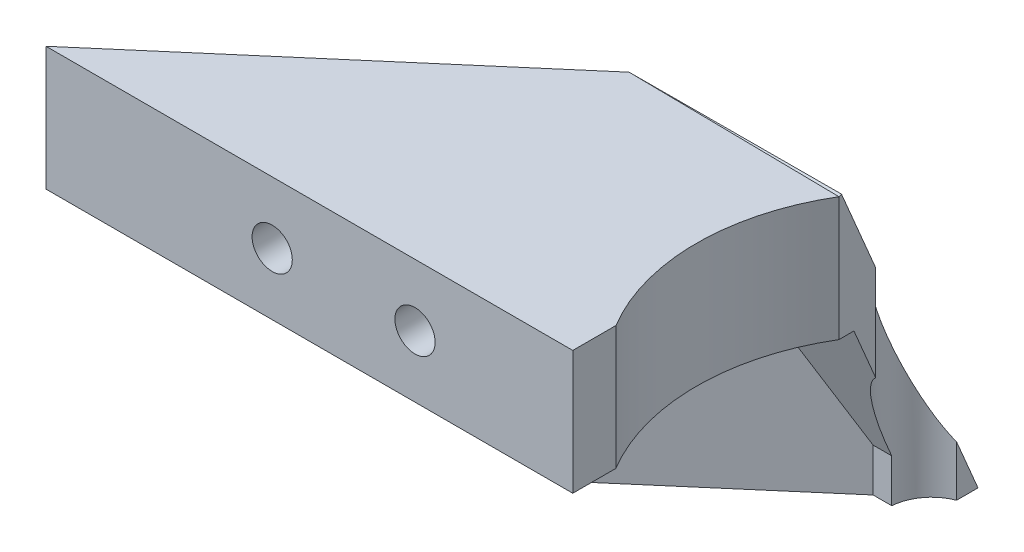
SolidWorks part; units mm, degrees
ref_plane "Alzado" through (0, 0, 0) normal (0, 0, 1) x (1, 0, 0)
ref_plane "Planta" through (0, 0, 0) normal (0, 1, 0) x (1, 0, 0)
ref_plane "Vista lateral" through (0, 0, 0) normal (1, 0, 0) x (0, 0, -1)
sketch "Croquis1" plane through (0, 0, 0) normal (0, 1, 0) x (1, 0, 0)
  line L0 (0, 20) -> (0, -20) construction
  line L1 (-20, 20) -> (20, 20)
  line L2 (-20, 20) -> (-20, -20)
  line L3 (-20, -20) -> (20, -20)
  line L4 (20, 20) -> (20, -20)
  line L5 (-20, 20) -> (20, -20) construction
  line L6 (-20, -20) -> (20, 20) construction
  line L7 (-20, -4.25) -> (-30, -7.25)
  line L8 (-30, -7.25) -> (-30, -15.25)
  line L9 (-30, -15.25) -> (30, -15.25)
  line L10 (20, -4.25) -> (30, -7.25)
  line L11 (30, -7.25) -> (30, -15.25)
  circle A0 centre (-15, 15) radius 2.125
  circle A1 centre (15, 15) radius 2.125
  circle A4 centre (0, 0) radius 15.25
  circle A5 centre (-15, -15) radius 2.125 [skipped]
  circle A6 centre (15, -15) radius 2.125 [skipped]
  point P0 (0, 0)
  point P25 (0, -15.25)
  dimension "D3" = 4.25
  dimension "D7" = 30.5
  dimension "D1" = 40
  dimension "D2" = 40
  dimension "D4" = 5
  dimension "D5" = 2
  dimension "D8" = 8
  dimension "D9" = 10
  dimension "D10" = 15.25
  dimension "D12" = 3
  dimension "D6" = 2
extrude "Soporte caja reductora" add sketch "Croquis1" against normal blind 20
sketch "Croquis3" plane through (0, 0, 15.25) normal (0, 0, 1) x (1, 0, 0)
  line L3 (-20, -20) -> (-20, 0) construction
  circle A0 centre (-23.5, -10) radius 2.125
  circle A1 centre (23.5, -10) radius 2.125
  dimension "D1" = 4.25
  dimension "D2" = 3.5
extrude "Cortar-Extruir1" cut sketch "Croquis3" against normal through all
fillet "Redondeo1" radius 5 2 edges at (-20, -10, -20) (20, -10, -20)
sketch "Sketch1" plane through (0, 0, 0) normal (0, 1, 0) x (1, 0, 0)
  line L0 (15, 20) -> (30, 20)
  line L1 (30, 20) -> (30, 8)
  line L2 (30, 8) -> (25.5, 8)
  line L4 (25.5, 8) -> (25.5, 15)
  line L5 (25.5, 15) -> (20, 15)
  circle A0 centre (15, 15) radius 5
  arc M37 (20, 15) -> (15, 20) centre (15, 15) ccw
  dimension "D1" = 12
  dimension "D2" = 5.5
extrude "Boss-Extrude1" add sketch "Sketch1" along direction (0, 1, 0) on the side against the normal up to surface (20 mm away) contours L5 L4 L2 L1 L0 M37
sketch "Sketch2" plane through (0, 0, -20) normal (0, 0, -1) x (-1, 0, 0)
  line L1 (-20, -20) -> (-20, 0) construction
  circle A0 centre (-22.75, -10) radius 1.625
  dimension "D1" = 3.25
  dimension "D2" = 2.75
extrude "Cut-Extrude1" cut sketch "Sketch2" against normal up to next
sketch "Sketch3" plane through (0, 0, -15) normal (0, 0, 1) x (1, 0, 0)
  line L1 (20, -11.5877) -> (22.75, -13.1754)
  line L2 (22.75, -13.1754) -> (25.5, -11.5877)
  line L3 (25.5, -11.5877) -> (25.5, -8.4123)
  line L4 (25.5, -8.4123) -> (22.75, -6.8246)
  line L5 (22.75, -6.8246) -> (20, -8.4123)
  line L6 (20, -8.4123) -> (20, -11.5877)
  circle A0 centre (22.75, -10) radius 2.75 construction
  dimension "D1" = 5.5
extrude "Cut-Extrude2" cut sketch "Sketch3" against normal blind 2
sketch "Sketch4" plane through (25.5, 0, 0) normal (-1, 0, 0) x (0, 0, 1)
  line L5 (-15, -8.4123) -> (-15, 0) construction
  line L6 (-20, 0) -> (-8, 0) construction
  circle A0 centre (-12.25, -10) radius 1.625
  dimension "D1" = 2.75
  dimension "D2" = 3.25
  dimension "D3" = 10
extrude "Cut-Extrude3" cut sketch "Sketch4" against normal through all
sketch "Sketch5" plane through (30, 0, 0) normal (1, 0, 0) x (0, 0, -1)
  line L1 (15, -11.5877) -> (15, -8.4123)
  line L2 (15, -8.4123) -> (12.25, -6.8246)
  line L3 (12.25, -6.8246) -> (9.5, -8.4123)
  line L4 (9.5, -8.4123) -> (9.5, -11.5877)
  line L5 (9.5, -11.5877) -> (12.25, -13.1754)
  line L6 (12.25, -13.1754) -> (15, -11.5877)
  circle A0 centre (12.25, -10) radius 2.75 construction
  dimension "D1" = 5.5
extrude "Cut-Extrude4" cut sketch "Sketch5" along normal blind 2 from surface
sketch "Croquis6" plane through (0, 0, 0) normal (0, 1, 0) x (1, 0, 0)
  line L0 (-20, -20) -> (20, -20) construction
  line L1 (-15.25, 0) -> (15.25, 0)
  line L2 (-15.25, 0) -> (-15.25, -20)
  line L3 (-15.25, -20) -> (15.25, -20)
  line L4 (15.25, 0) -> (15.25, -20)
  line L6 (-20, -20) -> (20, -20)
  line L7 (-20, -20) -> (-20, -15.25)
  line L8 (-20, -15.25) -> (20, -15.25)
  line L9 (20, -20) -> (20, -15.25)
  circle A0 centre (0, 0) radius 15.25 construction
  circle M5 centre (0, 0) radius 15.25
  line M14 (-20, -15.25) -> (-20, -20)
  line M15 (-20, -20) -> (20, -20)
  line M16 (20, -20) -> (20, -15.25)
extrude "Cortar-Extruir17" cut sketch "Croquis6" against normal through all contours L8 L2 L4 M15 | L8 L2 M14 M15 | L2 L8 M5 | L8 L4 M5 | L8 L4 M15 M16
mirror "Simetría1" about plane through (0, 0, 0) normal (0, 1, 0) of bodies 111
sketch "Croquis7" plane through (0, 0, -20) normal (0, 0, -1) x (-1, 0, 0)
  line L1 (-30, 0) -> (30, 0)
  line L2 (-30, 0) -> (-30, -20)
  line L3 (-30, -20) -> (30, -20)
  line L4 (30, 0) -> (30, -20)
extrude "Cortar-Extruir18" cut sketch "Croquis7" against normal through all
sketch "Croquis8" plane through (0, 20, 0) normal (0, 1, 0) x (1, 0, 0)
  line L3 (-15, 20) -> (30, 20) construction
  line L4 (-11.0405, 13.9391) -> (-10.3152, 11.2321)
  line L5 (10.8174, 13.8793) -> (10.3152, 11.2321)
  line L59 (10.8174, 13.8793) -> (11.9787, 20)
  line L60 (-11.0405, 13.9391) -> (-12.6645, 20)
  line L61 (11.9787, 20) -> (-12.6645, 20)
  circle A0 centre (0, 0) radius 15.25
extrude "Saliente-Extruir2" add sketch "Croquis8" along normal blind 49
sketch "Croquis9" plane through (0, 69, 0) normal (0, 1, 0) x (1, 0, 0)
  line L0 (-20, 0) -> (20, 0)
  line L1 (-20, 15) -> (-20, -4.25) construction
  line L2 (20, 15) -> (20, -4.25) construction
  line L3 (-20, 0) -> (-20, 15)
  line L4 (-15, 20) -> (12.6645, 20)
  line L5 (12.6645, 20) -> (20, 13.9368)
  line L6 (20, 13.9368) -> (20, 0)
  line L7 (20, 0) -> (20.1759, -0.147)
  line L8 (-14.75, 0) -> (-14.75, -15.25)
  line L9 (-15.25, -15.25) -> (-30, -15.25)
  line L10 (-30, -15.25) -> (-30, -7.25)
  line L11 (-30, -7.25) -> (-20, -4.25)
  line L12 (-20, -4.25) -> (-20, 0)
  line L13 (-14.75, -15.25) -> (-15.25, -15.25)
  line L14 (-14.75, -15.25) -> (0, -15.25)
  line L15 (0, -15.25) -> (0, -14.75)
  circle A0 centre (0, 0) radius 14.75
  circle A1 centre (-15, 15) radius 5
  dimension "D1" = 29.5
extrude "Soporte motor" add sketch "Croquis9" against normal blind 15 from offset 15 offset against normal yes
sketch "Croquis12" plane through (0, 0, 15.25) normal (0, 0, 1) x (1, 0, 0)
  line L1 (0, 54) -> (-30, 54) construction
  line L2 (-20, 39) -> (-20, 54) construction
  circle A0 centre (-23.5, 46.5) radius 2.125
  dimension "D3" = 4.25
  dimension "D1" = 7.5
  dimension "D2" = 3.5
extrude "Agujeros de sujecion a base" cut sketch "Croquis12" against normal through all
sketch "Croquis13" plane through (0, 0, 15.25) normal (0, 0, 1) x (1, 0, 0)
  line L1 (-20, 44.4793) -> (-20, 48.5207)
  line L2 (-20, 48.5207) -> (-23.5, 50.5415)
  line L3 (-23.5, 50.5415) -> (-27, 48.5207)
  line L4 (-27, 48.5207) -> (-27, 44.4793)
  line L5 (-27, 44.4793) -> (-23.5, 42.4585)
  line L6 (-23.5, 42.4585) -> (-20, 44.4793)
  circle A0 centre (-23.5, 46.5) radius 3.5 construction
  dimension "D1" = 7
extrude "Tuerca Agujero de sujecion a base" cut sketch "Croquis13" against normal blind 10 from offset 4 offset against normal yes
sketch "Croquis10" plane through (0, 69, 0) normal (0, 1, 0) x (1, 0, 0)
  line L0 (-10.3152, 11.2321) -> (-9.8079, 9.3388)
  line L1 (10.3152, 11.2321) -> (9.4813, 8.1201)
  circle A0 centre (0, 0) radius 14.75
  circle A1 centre (0, 0) radius 15.25
  arc M2 (-10.3152, 11.2321) -> (10.3152, 11.2321) centre (0, 0) cw
extrude "Saliente-Extruir4" add sketch "Croquis10" against normal up to surface (15 mm away) contours A0 L1 L0 M2
sketch "Croquis11" plane through (0, 0, 0) normal (0, -1, 0) x (1, 0, 0)
  line L0 (0, 0) -> (0, -12.6937) construction
  line L1 (15, -20) -> (30, -20)
  line L2 (30, -20) -> (30, 15.25)
  line L3 (30, 15.25) -> (15.25, 15.25)
  line L4 (15.25, 0) -> (15.25, 15.25) construction
  line L5 (15.25, 15.25) -> (30, 15.25) construction
  line L6 (15.25, 15.25) -> (15.25, 4.25)
  line L7 (15.25, 4.25) -> (20, 4.25)
  line L8 (20, 4.25) -> (20, -15)
  circle A0 centre (0, 0) radius 22.5
  circle A1 centre (-15, -15) radius 5
  circle A2 centre (15, -15) radius 5
  line M8 (-15, -20) -> (30, -20)
  line M9 (30, -20) -> (30, -8)
  line M10 (30, -8) -> (25.5, -8)
  line M11 (25.5, -8) -> (25.5, -15)
  line M12 (25.5, -15) -> (20, -15)
  line M14 (20, 4.25) -> (30, 7.25)
  line M15 (30, 7.25) -> (30, 15.25)
  line M16 (30, 15.25) -> (15.25, 15.25)
  line M17 (15.25, 15.25) -> (15.25, 0)
  dimension "D1" = 45
extrude "Cortar-Extruir19" cut sketch "Croquis11" against normal blind 25 contours A0 L3 L7 M14 M17 | A0 M14 M15 M16 | A2 M12 M8 M9 M10 M11
mirror "Simetría2"
sketch "Croquis14" plane through (0, 0, 15.25) normal (0, 0, 1) x (1, 0, 0)
  line L1 (-30, 20) -> (20, 20)
  line L2 (-30, 20) -> (-30, 138)
  line L3 (-30, 138) -> (20, 138)
  line L4 (20, 20) -> (20, 138)
extrude "Cortar-Extruir22" cut sketch "Croquis14" against normal through all
sketch "Croquis15" plane through (0, 0, 0) normal (0, -1, 0) x (1, 0, 0)
  line L0 (-30, 7.25) -> (-30, 15.25) construction
  line L1 (-20, 4.25) -> (-30, 4.25)
  line L2 (-20, 4.25) -> (-20, 11.25)
  line L3 (-20, 11.25) -> (-30, 11.25)
  line L4 (-30, 4.25) -> (-30, 11.25)
  line L5 (-30, 15.25) -> (-15.25, 15.25) construction
  dimension "D1" = 4
extrude "Cortar-Extruir23" cut sketch "Croquis15" against normal through all
sketch "Croquis16" plane through (0, 0, 0) normal (0, -1, 0) x (1, 0, 0)
  line L0 (-15.25, 0) -> (-15.25, 15.25) construction
  line L1 (-30, 15.25) -> (-15.25, 15.25)
  line L2 (-30, 15.25) -> (-30, 12.75)
  line L3 (-20, 12.75) -> (-15.25, 12.75)
  line L4 (-15.25, 15.25) -> (-15.25, 12.75)
  line L5 (-30, 12.75) -> (-30, 11.25)
  line L6 (-30, 11.25) -> (-20, 11.25)
  line L7 (-20, 11.25) -> (-30, 11.25) construction
  line L8 (-20, -15) -> (-20, 11.25) construction
  line L9 (-20, 11.25) -> (-20, 12.75)
  dimension "D1" = 2.5
extrude "Cortar-Extruir24" cut sketch "Croquis16" against normal through all
sketch "Croquis18" plane through (0, 0, -20) normal (0, 0, -1) x (-1, 0, 0)
  line L0 (20, 0) -> (20, 20) construction
  line L1 (-20, 0) -> (20, 0)
  line L2 (-20, 0) -> (-20, 10)
  line L3 (-20, 10) -> (20, 10)
  line L4 (20, 0) -> (20, 10)
  line L5 (15, 20) -> (-15, 20) construction
  dimension "D1" = 10
extrude "Cortar-Extruir25" cut sketch "Croquis18" against normal through all
sketch "Croquis19" plane through (0, 20, 0) normal (0, 1, 0) x (1, 0, 0)
  line L0 (-20, -12.75) -> (-34, -12.75)
  line L1 (-34, -12.75) -> (-34, -7.75)
  line L2 (-34, -7.75) -> (-24, -7.75)
  line L3 (-24, -7.75) -> (-20, -3.75)
  line L4 (-20, 15) -> (-20, -12.75) construction
  line L5 (-20, -3.75) -> (-20, -12.75)
  dimension "D1" = 5
  dimension "D2" = 4
  dimension "D3" = 4
  dimension "D4" = 10
extrude "Saliente-Extruir5" add sketch "Croquis19" against normal up to surface (10 mm away) up to face at (15, 10, -12.875)
sketch "Croquis20" plane through (0, 0, 7.75) normal (0, 0, -1) x (-1, 0, 0)
  circle A0 centre (29, 15) radius 1
  dimension "D1" = 2
extrude "Cortar-Extruir26" cut sketch "Croquis20" against normal through all
sketch "Croquis21" plane through (20, 0, 0) normal (1, 0, 0) x (0, 0, -1)
  line L1 (20, 20) -> (20, 10) construction
  circle A0 centre (4.75, 15) radius 1.625
  dimension "D1" = 3.25
  dimension "D2" = 15.25
extrude "Cortar-Extruir27" cut sketch "Croquis21" against normal up to next
sketch "Croquis22" plane through (0, 10, 0) normal (0, -1, 0) x (1, 0, 0)
  circle A0 centre (-15, -15) radius 2.125
  circle A1 centre (15, -15) radius 2.125
  circle A2 centre (15, -15) radius 1
  circle A3 centre (-15, -15) radius 1
  dimension "D1" = 2
extrude "Saliente-Extruir6" add sketch "Croquis22" against normal blind 10
sketch "Croquis23" plane through (0, 0, -20) normal (0, 0, -1) x (-1, 0, 0)
  circle A0 centre (0, 15) radius 1.625
  dimension "D1" = 3.25
extrude "Cortar-Extruir28" cut sketch "Croquis23" against normal through all
sketch "Croquis24" plane through (0, 0, -20) normal (0, 0, -1) x (-1, 0, 0)
  line L1 (1.5877, 12.25) -> (3.1754, 15)
  line L2 (3.1754, 15) -> (1.5877, 17.75)
  line L3 (1.5877, 17.75) -> (-1.5877, 17.75)
  line L4 (-1.5877, 17.75) -> (-3.1754, 15)
  line L5 (-3.1754, 15) -> (-1.5877, 12.25)
  line L6 (-1.5877, 12.25) -> (1.5877, 12.25)
  circle A0 centre (0, 15) radius 2.75 construction
  dimension "D1" = 5.5
extrude "Cortar-Extruir29" cut sketch "Croquis24" against normal blind 10 from offset 3 offset against normal yes
sketch "Croquis26" plane through (0, 10, 0) normal (0, -1, 0) x (1, 0, 0)
  line L0 (-29, 12.75) -> (-58.825, 12.75)
  line L1 (-58.825, 12.75) -> (-39.1605, -4.1045)
  line L3 (-39.5945, 1.5357) -> (-46.8449, 7.75)
  line L4 (-46.8449, 7.75) -> (-34.2682, 7.75)
  line L5 (-34.2682, 7.75) -> (-39.5945, 1.5357)
  line L7 (-29, 7.75) -> (-35.7321, -0.1045)
  line L8 (-29, 7.75) -> (-29, 12.75)
  line L9 (-34, 7.75) -> (-24, 7.75) construction
  line L10 (-34, 12.75) -> (-15.25, 12.75) construction
  line L11 (-39.1605, -4.1045) -> (-20, -4.1045)
  line L12 (-20, 3.75) -> (-20, -15) construction
  line L13 (-20, -4.1045) -> (-20, -0.1045)
  line L14 (-20, -0.1045) -> (-35.7321, -0.1045)
  dimension "D1" = 4
  dimension "D2" = 4
  dimension "D3" = 4
  dimension "D4" = 29.825
  dimension "D5" = 40.6
extrude "Saliente-Extruir7" add sketch "Croquis26" against normal blind 10
sketch "Croquis27" plane through (0, 0, 12.75) normal (0, 0, 1) x (1, 0, 0)
  line L0 (-29, 16) -> (-29, 14) construction
  line L1 (-46.8449, 20) -> (-46.8449, 10) construction
  circle A0 centre (-40.5449, 15) radius 1.625
  circle A2 centre (-29, 15) radius 1.625
  dimension "D1" = 3.25
  dimension "D2" = 6.3
extrude "Cortar-Extruir30" cut sketch "Croquis27" against normal up to next
sketch "Croquis28" plane through (0, 0, 12.75) normal (0, 0, 1) x (1, 0, 0)
  line L1 (-38.9572, 12.25) -> (-37.3694, 15)
  line L2 (-37.3694, 15) -> (-38.9572, 17.75)
  line L3 (-38.9572, 17.75) -> (-42.1326, 17.75)
  line L4 (-42.1326, 17.75) -> (-43.7203, 15)
  line L5 (-43.7203, 15) -> (-42.1326, 12.25)
  line L6 (-42.1326, 12.25) -> (-38.9572, 12.25)
  line L7 (-27.4123, 12.25) -> (-25.8246, 15)
  line L8 (-25.8246, 15) -> (-27.4123, 17.75)
  line L9 (-27.4123, 17.75) -> (-30.5877, 17.75)
  line L10 (-30.5877, 17.75) -> (-32.1754, 15)
  line L11 (-32.1754, 15) -> (-30.5877, 12.25)
  line L12 (-30.5877, 12.25) -> (-27.4123, 12.25)
  circle A0 centre (-40.5449, 15) radius 2.75 construction
  circle A1 centre (-29, 15) radius 2.75 construction
  dimension "D1" = 5.5
extrude "Cortar-Extruir31" cut sketch "Croquis28" against normal up to next from offset 3 offset against normal yes
sketch "Croquis29" plane through (-18.6128, 0, -21.716) normal (-0.6508, 0, -0.7593) x (-0.7593, 0, 0.6508)
  line L2 (31.0624, 20) -> (31.0624, 10) construction
  circle A0 centre (33.8124, 15) radius 1.625
  dimension "D2" = 3.25
  dimension "D1" = 2.75
extrude "Cortar-Extruir32" cut sketch "Croquis29" against normal up to next
sketch "Croquis31" plane through (-18.6128, 0, -21.716) normal (-0.6508, 0, -0.7593) x (-0.7593, 0, 0.6508)
  line L1 (36.5624, 16.5877) -> (33.8124, 18.1754)
  line L2 (33.8124, 18.1754) -> (31.0624, 16.5877)
  line L3 (31.0624, 16.5877) -> (31.0624, 13.4123)
  line L4 (31.0624, 13.4123) -> (33.8124, 11.8246)
  line L5 (33.8124, 11.8246) -> (36.5624, 13.4123)
  line L6 (36.5624, 13.4123) -> (36.5624, 16.5877)
  circle A0 centre (33.8124, 15) radius 2.75 construction
  dimension "D1" = 5.5
extrude "Cortar-Extruir33" cut sketch "Croquis31" against normal up to next from offset 2.5 offset against normal yes
sketch "Croquis35" plane through (0, 20, 0) normal (0, 1, 0) x (1, 0, 0)
  line L0 (-15, 20) -> (15, 20) construction
  line L1 (10.3896, 0) -> (23.695, 0)
  line L2 (10.3896, 0) -> (10.3896, -6.8269)
  line L3 (10.3896, -6.8269) -> (23.695, -6.8269)
  line L4 (23.695, 0) -> (23.695, -6.8269)
  dimension "D1" = 20
extrude "Cortar-Extruir34" cut sketch "Croquis35" against normal through all both and the other way through all
sketch "Croquis36" plane through (20, 0, 0) normal (1, 0, 0) x (0, 0, -1)
  line L1 (7.5, 16.5877) -> (4.75, 18.1754)
  line L2 (4.75, 18.1754) -> (2, 16.5877)
  line L3 (2, 16.5877) -> (2, 13.4123)
  line L4 (2, 13.4123) -> (4.75, 11.8246)
  line L5 (4.75, 11.8246) -> (7.5, 13.4123)
  line L6 (7.5, 13.4123) -> (7.5, 16.5877)
  circle A0 centre (4.75, 15) radius 2.75 construction
  dimension "D1" = 5.5
extrude "Cortar-Extruir35" cut sketch "Croquis36" against normal blind 10 from offset 3 offset against normal yes
sketch "Croquis37" plane through (0, 10, 0) normal (0, -1, 0) x (1, 0, 0)
  line L0 (-39.1605, -4.1045) -> (-20.6149, -20)
  line L1 (-20.6149, -20) -> (-15, -20)
  line L2 (-33.014, -4.1045) -> (-19.5581, -15.6376)
  line L3 (-39.1605, -4.1045) -> (-20, -4.1045) construction
  line L4 (-19.5581, -15.6376) -> (-15, -20)
  line L5 (-58.825, 12.75) -> (-39.1605, -4.1045) construction
  line L6 (-39.5945, 1.5357) -> (-46.8449, 7.75) construction
  line L7 (-39.1605, -4.1045) -> (-33.014, -4.1045)
extrude "Saliente-Extruir8" add sketch "Croquis37" against normal blind 10
sketch "Croquis38" plane through (0, 10, 0) normal (0, -1, 0) x (1, 0, 0)
  line L0 (-58.825, 12.75) -> (-38.825, 12.75)
  line L1 (-58.825, 12.75) -> (-15.25, 12.75) construction
  line L2 (-38.825, 12.75) -> (-38.825, 9.75)
  line L3 (-38.825, 9.75) -> (-55.3248, 9.75)
  line L4 (-58.825, 12.75) -> (-20.6149, -20) construction
  line L5 (-55.3248, 9.75) -> (-58.825, 12.75)
  dimension "D1" = 3
  dimension "D2" = 20
extrude "Saliente-Extruir9" add sketch "Croquis38" along normal blind 13
sketch "Croquis39" plane through (0, 10, 0) normal (0, -1, 0) x (1, 0, 0)
  line L0 (-38.825, 9.75) -> (-38.825, 7.75)
  line L1 (-46.8449, 7.75) -> (-34.2682, 7.75) construction
  line L3 (-55.3248, 9.75) -> (-20.6149, -20) construction
  line L4 (-52.9914, 7.75) -> (-55.3248, 9.75)
  line L5 (-55.3248, 9.75) -> (-38.825, 9.75)
  line L6 (-52.9914, 7.75) -> (-50.658, 5.75)
  line L7 (-50.658, 5.75) -> (-38.825, 5.75)
  line L8 (-38.825, 5.75) -> (-38.825, 7.75)
  dimension "D1" = 2
extrude "Saliente-Extruir10" add sketch "Croquis39" along normal blind 3
mirror "Simetría3" of bodies 142
sketch "Croquis40" plane through (0, 0, -20) normal (0, 0, -1) x (-1, 0, 0)
  line L1 (-30.8963, 20) -> (75.6873, 20)
  line L2 (-30.8963, 20) -> (-30.8963, -27.3915)
  line L3 (-30.8963, -27.3915) -> (75.6873, -27.3915)
  line L4 (75.6873, 20) -> (75.6873, -27.3915)
extrude "Cortar-Extruir36" cut sketch "Croquis40" against normal through all both and the other way through all
sketch "Croquis41" plane through (0, 0, -20) normal (0, 0, -1) x (-1, 0, 0)
  line L1 (38.825, 30) -> (63.3839, 30)
  line L2 (38.825, 30) -> (38.825, 48.2062)
  line L3 (38.825, 48.2062) -> (63.3839, 48.2062)
  line L4 (63.3839, 30) -> (63.3839, 48.2062)
extrude "Cortar-Extruir37" cut sketch "Croquis41" against normal through all both and the other way through all
sketch "Croquis42" plane through (0, 20, 0) normal (0, -1, 0) x (1, 0, 0)
  line L0 (-58.825, 12.75) -> (-15.25, 12.75) construction
  line L1 (-16.25, 12.75) -> (23.5436, 12.75)
  line L2 (-16.25, 12.75) -> (-16.25, -23.8027)
  line L3 (-16.25, -23.8027) -> (23.5436, -23.8027)
  line L4 (23.5436, 12.75) -> (23.5436, -23.8027)
  line L5 (-15.25, 12.75) -> (-15.25, 0) construction
  dimension "D1" = 1
extrude "Cortar-Extruir38" cut sketch "Croquis42" against normal through all both and the other way through all
sketch "Croquis43" plane through (0, 20, 0) normal (0, -1, 0) x (1, 0, 0)
  line L0 (-46.8449, 7.75) -> (-19.5619, 7.75)
  line L1 (-19.5619, 7.75) -> (-19.5619, -16.3714)
  line L2 (-19.5619, -16.3714) -> (-46.8449, 7.75)
extrude "Saliente-Extruir11" add sketch "Croquis43" against normal blind 3
sketch "Croquis44" plane through (0, 30, 0) normal (0, 1, 0) x (1, 0, 0)
  line L0 (-58.825, -12.75) -> (-16.25, -12.75) construction
  line L1 (-16.25, -12.75) -> (-16.25, 20) construction
  circle A0 centre (-1.25, -0.25) radius 17.5
  dimension "D1" = 35
  dimension "D2" = 12.5
  dimension "D3" = 15
extrude "Cortar-Extruir39" cut sketch "Croquis44" against normal through all both and the other way through all
sketch "Croquis45" plane through (0, 30, 0) normal (0, 1, 0) x (1, 0, 0)
  line L0 (-33.014, 4.1045) -> (-39.1605, 4.1045)
  line L1 (-58.825, -12.75) -> (-20.6149, 20) construction
  line L2 (-39.1605, 4.1045) -> (-20.6149, 20)
  line L3 (-20.6149, 20) -> (-16.25, 20)
  line L4 (-16.25, 20) -> (-16.25, 15.2649)
  line L5 (-33.014, 4.1045) -> (-19.993, 15.2649)
  line L6 (-19.993, 15.2649) -> (-16.25, 15.2649)
extrude "Saliente-Extruir12" add sketch "Croquis45" along normal blind 16
sketch "Croquis46" plane through (-16.25, 0, 0) normal (1, 0, 0) x (0, 0, -1)
  line L0 (9, 20) -> (20, 46)
  line L1 (-12.75, 20) -> (20, 20) construction
  line L2 (20, 46) -> (20, 20)
  line L3 (20, 20) -> (9, 20)
  dimension "D1" = 11
extrude "Cortar-Extruir40" cut sketch "Croquis46" against normal through all
sketch "Croquis47" plane through (0, -0.1932, -0.4567) normal (0, -0.3896, -0.921) x (-1, 0, 0)
  line L5 (16.25, 21.8341) -> (33.4488, 21.9261)
  line L6 (33.4488, 21.9261) -> (22.7201, 45.5265)
  line L7 (33.4488, 21.9261) -> (20.6149, 50.1573) construction
  line L8 (22.7201, 45.5265) -> (16.25, 45.5265)
  line L9 (16.25, 50.1573) -> (16.25, 38.0047) construction
  line L10 (16.25, 45.5265) -> (16.25, 21.8341)
extrude "Saliente-Extruir14" add sketch "Croquis47" against normal blind 3
sketch "Croquis48" plane through (0, 20, 0) normal (0, -1, 0) x (1, 0, 0)
  circle A0 centre (-1.25, 0.25) radius 17.5
extrude "Cortar-Extruir41" cut sketch "Croquis48" against normal through all both and the other way through all
sketch "Croquis49" plane through (0, 20, 0) normal (0, -1, 0) x (1, 0, 0)
  line L0 (-16.25, -20) -> (-16.25, -8.9642) construction
  line L1 (-16.25, -20) -> (-20.6149, -20) construction
  circle A0 centre (-15, -15) radius 3.5
  dimension "D1" = 7
  dimension "D2" = 1.25
  dimension "D3" = 5
extrude "Cortar-Extruir42" cut sketch "Croquis49" against normal through all
mirror "Simetría4" about plane through (0, 46, 0) normal (0, -1, 0) of bodies 153
sketch "Croquis50" plane through (-18.6128, 0, -21.716) normal (-0.6508, 0, -0.7593) x (-0.7593, 0, 0.6508)
  line L1 (62.2327, 46) -> (-33.5441, 46)
  line L2 (62.2327, 46) -> (62.2327, -5.6613)
  line L3 (62.2327, -5.6613) -> (-33.5441, -5.6613)
  line L4 (-33.5441, 46) -> (-33.5441, -5.6613)
extrude "Cortar-Extruir43" cut sketch "Croquis50" against normal through all both and the other way through all
